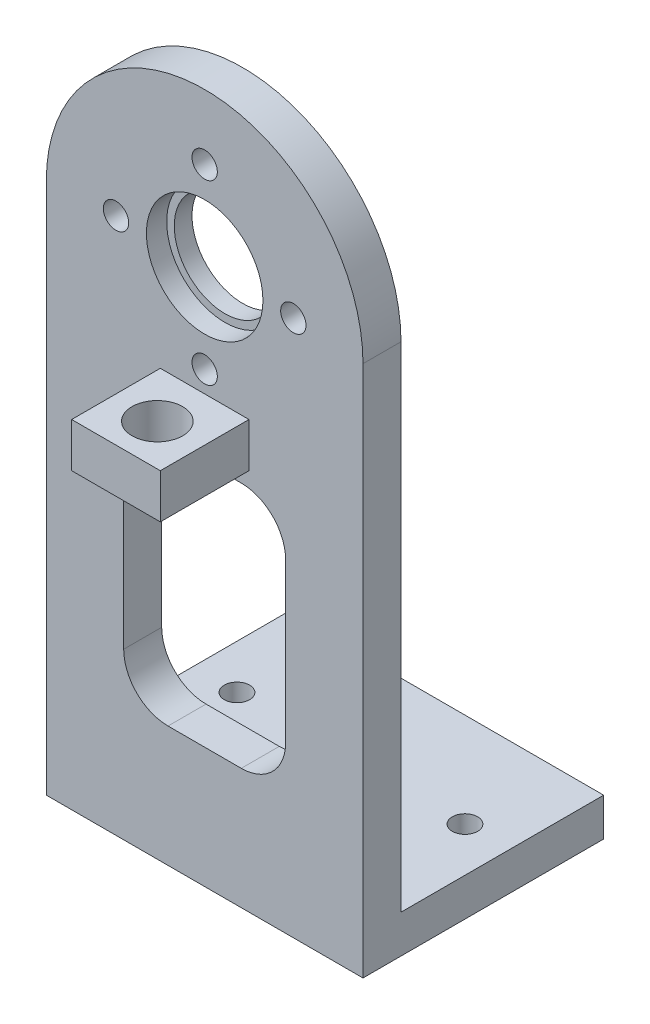
SolidWorks part; units mm, degrees
material "ABS"
ref_plane "Front Plane" through (0, 0, 0) normal (0, 0, 1) x (1, 0, 0)
ref_plane "Top Plane" through (0, 0, 0) normal (0, 1, 0) x (1, 0, 0)
ref_plane "Right Plane" through (0, 0, 0) normal (1, 0, 0) x (0, 0, -1)
sketch "Sketch1" plane through (0, 0, 0) normal (0, 0, 1) x (1, 0, 0)
  line L0 (-12.5, -11.1228) -> (12.5, -11.1228)
  line L1 (-12.5, 27.4354) -> (12.5, 27.4354)
  line L2 (-12.5, 27.4354) -> (-12.5, -14.5646)
  line L3 (-12.5, -14.5646) -> (12.5, -14.5646)
  line L4 (12.5, 27.4354) -> (12.5, -14.5646)
  arc A0 (12.5, 27.4354) -> (-12.5, 27.4354) centre (0, 27.4354) ccw
  point P0 (0, 0)
  dimension "D2" = 3.4418
  dimension "D1" = 25
  dimension "D3" = 42
extrude "Boss-Extrude1" add sketch "Sketch1" along normal blind 3 contours L4 L1 L2 L0 | L1 A0 | L4 L0 L2 L3
sketch "Sketch2" plane through (0, 0, 3) normal (0, 0, 1) x (1, 0, 0)
  circle A0 centre (0, 27.802) radius 4.6
  circle A1 centre (0, 27.802) radius 4
  circle A2 centre (0, 27.802) radius 7
  circle A3 centre (0, 34.802) radius 1
  circle A4 centre (7, 27.802) radius 1
  circle A5 centre (0, 20.802) radius 1
  circle A6 centre (-7, 27.802) radius 1
  dimension "D1" = 2
  dimension "D2" = 2
  dimension "D3" = 2
  dimension "D4" = 2
  dimension "D5" = 8
  dimension "D6" = 9.2
  dimension "D7" = 14
extrude "Cut-Extrude1" cut sketch "Sketch2" against normal blind 3 contours A2 A4 | A2 A4 | A2 A3 | A2 A3 | A2 A6 | A2 A6 | A2 A5 | A1
sketch "Sketch4" plane through (0, 0, 3) normal (0, 0, 1) x (1, 0, 0)
  circle A0 centre (0, 27.802) radius 4.6
  dimension "D1" = 9.2
extrude "Cut-Extrude2" cut sketch "Sketch4" against normal blind 1.6 contours A0
sketch "Sketch5" plane through (0, 0, 3) normal (0, 0, 1) x (1, 0, 0)
  line L0 (-12.5, -11.5646) -> (12.5, -11.5646)
  line L1 (-12.5, 27.4354) -> (-12.5, -14.5646) construction
  line L2 (12.5, 27.4354) -> (12.5, -14.5646) construction
  line L3 (-12.5, -14.5646) -> (12.5, -14.5646) construction
  line L7 (12.5, -14.5646) -> (12.5, 27.4354)
  line L8 (-12.5, 27.4354) -> (-12.5, -14.5646)
  line L9 (-12.5, -14.5646) -> (12.5, -14.5646)
  line L10 (12.5, -14.5646) -> (12.5, -11.5646)
  line L11 (-12.5, -11.5646) -> (-12.5, -14.5646)
  line L12 (-12.5, -14.5646) -> (12.5, -14.5646)
  arc A1 (12.5, 27.4354) -> (-12.5, 27.4354) centre (0, 27.4354) ccw
  dimension "D1" = 3
  dimension "D2" = 0
extrude "Boss-Extrude3" add sketch "Sketch5" against normal blind 19 contours L0 L10 L12 L11
sketch "Sketch7" plane through (0, -11.5646, 0) normal (0, 1, 0) x (1, 0, 0)
  line L0 (12.5, 16) -> (12.5, 0) construction
  line L1 (-12.5, 16) -> (-12.5, 0) construction
  line L2 (-12.5, 0) -> (12.5, 0) construction
  circle A0 centre (9, 8.55) radius 1
  circle A1 centre (-9, 8.55) radius 1
  dimension "D3" = 2
  dimension "D4" = 2
  dimension "D1" = 3.5
  dimension "D2" = 3.5
  dimension "D5" = 8.55
extrude "Cut-Extrude4" cut sketch "Sketch7" against normal blind 4
sketch "Sketch8" plane through (0, 0, 3) normal (0, 0, 1) x (1, 0, 0)
  line L1 (-6.3919, 14.467) -> (6.3919, 14.467)
  line L2 (-6.3919, 14.467) -> (-6.3919, -5.033)
  line L3 (-6.3919, -5.033) -> (6.3919, -5.033)
  line L4 (6.3919, 14.467) -> (6.3919, -5.033)
  point P0 (0, 4.717)
  dimension "D1" = 19.5
extrude "Cut-Extrude5" cut sketch "Sketch8" against normal blind 4 contours L4 L1 L2 L3
fillet "Fillet1" radius 3.5 4 edges at (-6.3919, -5.033, 1.5) (6.3919, -5.033, 1.5) (6.3919, 14.467, 1.5) (-6.3919, 14.467, 1.5)
sketch "Sketch9" plane through (0, 0, 3) normal (0, 0, 1) x (1, 0, 0)
  line L0 (-12.5, 27.4354) -> (-12.5, -14.5646) construction
  line L1 (12.5, 27.4354) -> (12.5, -14.5646) construction
  line L2 (-3.5, 19.1193) -> (3.5, 19.1193)
  line L3 (-3.5, 19.1193) -> (-3.5, 15.6193)
  line L4 (-3.5, 15.6193) -> (3.5, 15.6193)
  line L5 (3.5, 19.1193) -> (3.5, 15.6193)
  line L6 (-3.5, 19.1193) -> (3.5, 15.6193) construction
  line L7 (-3.5, 15.6193) -> (3.5, 19.1193) construction
  line L8 (-12.5, -14.5646) -> (12.5, -14.5646) construction
  arc A1 (12.5, 27.4354) -> (-12.5, 27.4354) centre (0, 27.4354) ccw construction
  point P0 (-8.07, 22.8654)
  point P1 (0, 17.3693)
  dimension "D4" = 3.5
  dimension "D1" = 7
  dimension "D2" = 12.5
  dimension "D3" = 12.5
extrude "Boss-Extrude4" add sketch "Sketch9" along normal blind 7 contours L4 L5 L2 L3
sketch "Sketch11" plane through (0, 19.1193, 0) normal (0, 1, 0) x (1, 0, 0)
  line L0 (-3.5, -10) -> (-3.5, -3) construction
  circle A0 centre (0, -6.7357) radius 2
  dimension "D1" = 4
  dimension "D2" = 3.5
extrude "Cut-Extrude6" cut sketch "Sketch11" against normal blind 10
